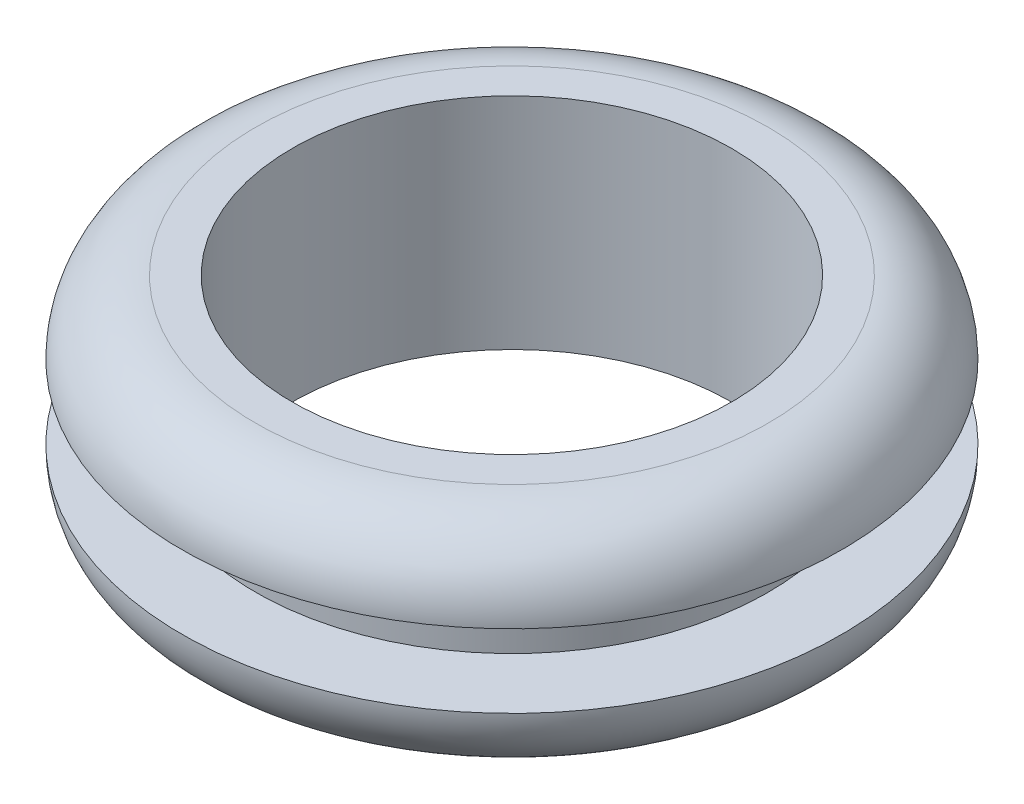
SolidWorks part; units mm, degrees
ref_plane "Front" through (0, 0, 0) normal (0, 0, 1) x (1, 0, 0)
ref_plane "Top" through (0, 0, 0) normal (0, 1, 0) x (1, 0, 0)
ref_plane "Right" through (0, 0, 0) normal (1, 0, 0) x (0, 0, -1)
sketch "Sketch1" plane through (0, 0, 0) normal (1, 0, 0) x (0, 0, -1)
  line L0 (0, -4.7625) -> (0, 4.7625) construction
  line L1 (0, 1.5875) -> (0, -1.5875) construction
  line L2 (-14.2875, 4.7625) -> (14.2875, 4.7625) construction
  line L3 (-9.525, 1.5875) -> (9.525, 1.5875) construction
  line L4 (-11.1125, 0) -> (11.1125, 0) construction
  point P12 (-9.525, 1.5875)
  point P13 (9.525, 1.5875)
  point P14 (-11.1125, 0)
  point P15 (11.1125, 0)
  point P16 (-14.2875, 4.7625)
  point P17 (0, -4.7625)
  point P18 (14.2875, 4.7625)
  point P19 (0, 4.7625)
  point P20 (0, 1.5875)
  point P21 (0, -1.5875)
  dimension "Overall Height E" = 9.525
  dimension "Material Thickness B" = 3.175
  dimension "Flange Diameter D" = 28.575
  dimension "ID C" = 19.05
  dimension "For ID A" = 22.225
sketch "Sketch2" plane through (0, 0, 0) normal (1, 0, 0) x (0, 0, -1)
  line L0 (-9.525, -4.7625) -> (-9.525, 4.7625)
  line L1 (-9.525, 4.7625) -> (-11.1125, 4.7625)
  line L2 (-11.1125, 1.5875) -> (-11.1125, -1.5875)
  line L3 (-11.1125, 1.5875) -> (-14.2875, 1.5875)
  line L4 (-11.1125, -1.5875) -> (-14.2875, -1.5875)
  line L5 (-9.525, -4.7625) -> (-11.1125, -4.7625)
  arc A0 (-14.2875, 1.5875) -> (-11.1125, 4.7625) centre (-11.1125, 1.5875) cw
  arc A1 (-14.2875, -1.5875) -> (-11.1125, -4.7625) centre (-11.1125, -1.5875) ccw
  point P4 (-14.2875, 1.5875)
revolve "Revolve1" add sketch "Sketch2" angle 360 about L0
ref_plane "Plane1" through (0, 4.7625, 0) normal (0, -1, 0) x (0, 0, -1)
sketch "Sketch3" plane through (0, 4.7625, 0) normal (0, -1, 0) x (0, 0, -1)
  line L0 (0, -14.2875) -> (0, 14.2875) construction
  line L1 (-14.2875, 0) -> (14.2875, 0) construction
  line L2 (0, 9.525) -> (0, -9.525) construction
  line L3 (-9.525, 0) -> (9.525, 0) construction
  line L4 (0, 11.1125) -> (0, -11.1125) construction
  line L5 (-11.1125, 0) -> (11.1125, 0) construction
  point P11 (0, 14.2875)
  point P12 (0, 9.525)
  point P13 (0, -9.525)
  point P14 (0, -14.2875)
  point P19 (0, -11.1125)
  point P20 (0, 11.1125)
